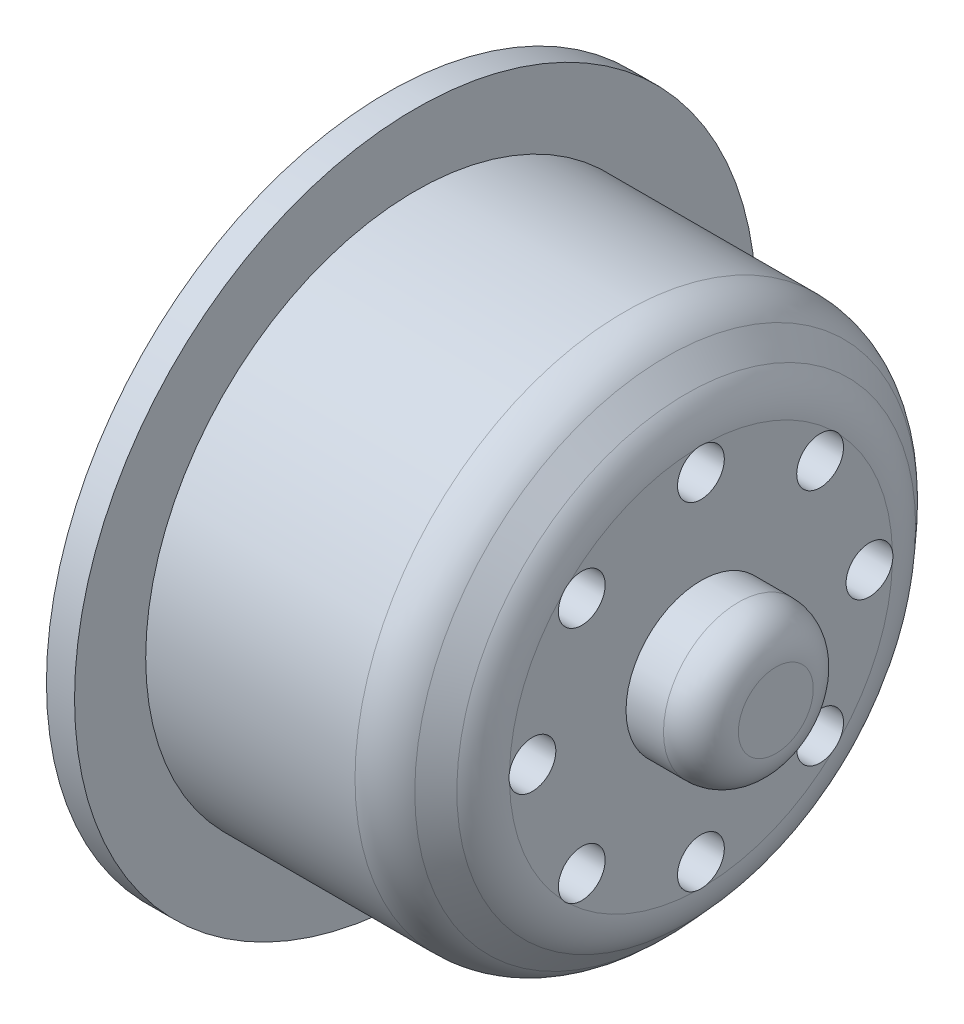
SolidWorks part; units mm, degrees
ref_plane "Front Plane" through (0, 0, 0) normal (0, 0, 1) x (1, 0, 0)
ref_plane "Top Plane" through (0, 0, 0) normal (0, 1, 0) x (1, 0, 0)
ref_plane "Right Plane" through (0, 0, 0) normal (1, 0, 0) x (0, 0, -1)
sketch "Sketch1" plane through (0, 0, 0) normal (0, 1, 0) x (1, 0, 0)
  line L0 (-12.3913, 0) -> (21, 0) construction
  line L1 (-4.6304, 14.4) -> (7.8696, 14.4)
  line L5 (13.3727, 0) -> (-6.1304, 0)
  line L8 (10.6196, 4) -> (14.6196, 4)
  line L9 (14.6196, 4) -> (14.6196, 0)
  line L10 (14.6196, 0) -> (13.3727, 0)
  line L11 (-4.6304, 14.4) -> (-4.6304, 18.2)
  line L12 (-4.6304, 18.2) -> (-6.1304, 18.2)
  line L13 (-6.1304, 18.2) -> (-6.1304, 0)
  line L15 (7.8696, 14.4) -> (10.6196, 11.3905)
  line L17 (10.6196, 11.3905) -> (10.6196, 4)
  point P6 (14.0015, 17.106)
  dimension "D2" = 132.42
  dimension "D3" = 4.0767
  dimension "D4" = 12.5
  dimension "D5" = 28.8
  dimension "D6" = 3.0095
  dimension "D7" = 4
  dimension "D8" = 8
  dimension "D9" = 3.8
  dimension "D10" = 1.5
  dimension "D11" = 11.3905
revolve "Revolve1" add sketch "Sketch1" angle 360 about L0
fillet "Fillet1" radius 2 1 edges at (14.6196, 0, 4)
sketch "Sketch4" plane through (-6.1304, 0, 0) normal (-1, 0, 0) x (0, 0, 1)
  circle A0 centre (0, 0) radius 5.6
  dimension "D1" = 11.2
extrude "Cut-Extrude3" cut sketch "Sketch4" against normal blind 6
sketch "Sketch5" plane through (10.6196, 0, 0) normal (1, 0, 0) x (0, 0, -1)
  circle A0 centre (0, 0) radius 9 construction
  circle A1 centre (0, 9) radius 1.25
  circle A2 centre (6.364, 6.364) radius 1.25
  circle A3 centre (9, 0) radius 1.25
  circle A4 centre (6.364, -6.364) radius 1.25
  circle A5 centre (0, -9) radius 1.25
  circle A6 centre (-6.364, -6.364) radius 1.25
  circle A7 centre (-9, 0) radius 1.25
  circle A8 centre (-6.364, 6.364) radius 1.25
  point P22 (0, 0)
  dimension "D1" = 18
  dimension "D2" = 2.5
  dimension "D3" = 8
extrude "Cut-Extrude4" cut sketch "Sketch5" against normal up to surface (16.75 mm away) up to face at (-6.1304, 0, 5.6)
sketch "Sketch6" plane through (-6.1304, 0, 0) normal (-1, 0, 0) x (0, 0, 1)
  circle A0 centre (0, 0) radius 9 construction
  circle A1 centre (0, 9) radius 2.5
  circle A2 centre (6.364, 6.364) radius 2.5
  circle A3 centre (9, 0) radius 2.5
  circle A4 centre (6.364, -6.364) radius 2.5
  circle A5 centre (0, -9) radius 2.5
  circle A6 centre (-6.364, -6.364) radius 2.5
  circle A7 centre (-9, 0) radius 2.5
  circle A8 centre (-6.364, 6.364) radius 2.5
  point P22 (0, 0)
  dimension "D1" = 18
  dimension "D2" = 5
  dimension "D3" = 8
extrude "Cut-Extrude5" cut sketch "Sketch6" against normal offset from surface (11.75 mm away) 5 up to face at (10.6196, 9, -1.25)
fillet "Fillet2" radius 3 2 edges at (10.6196, 0, 11.3905) (7.8696, 0, 14.4)
